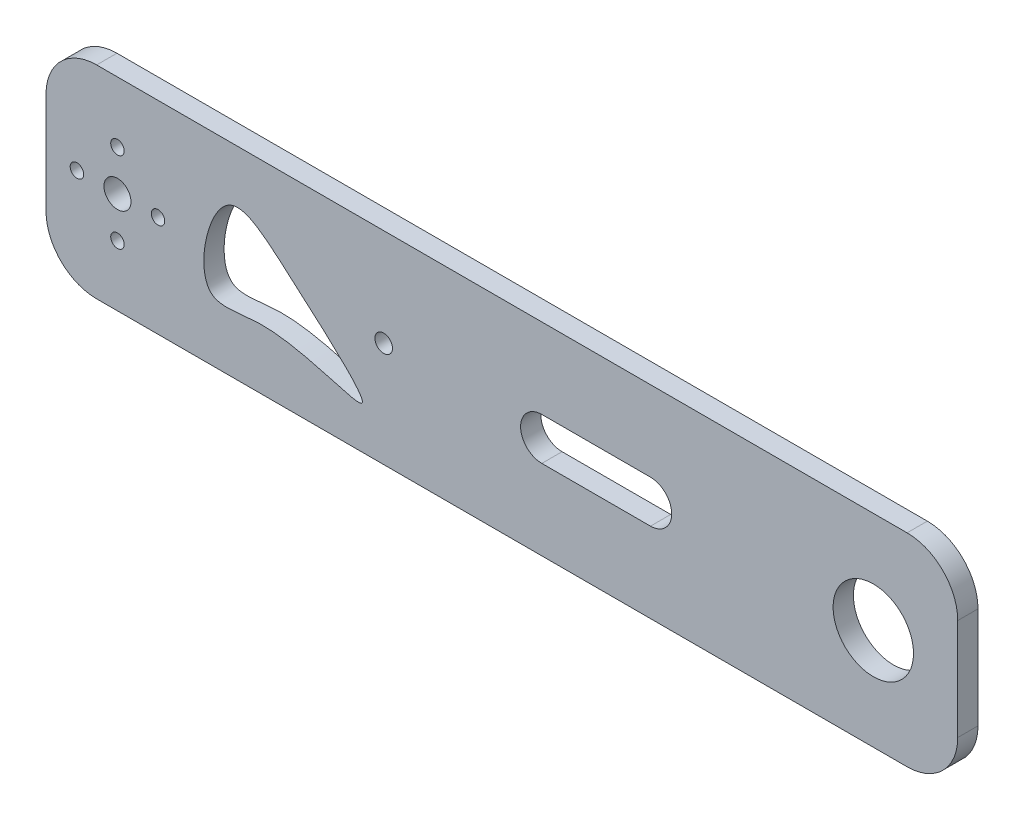
SolidWorks part; units mm, degrees
ref_plane "Front Plane" through (0, 0, 0) normal (0, 0, 1) x (1, 0, 0)
ref_plane "Top Plane" through (0, 0, 0) normal (0, 1, 0) x (1, 0, 0)
ref_plane "Right Plane" through (0, 0, 0) normal (1, 0, 0) x (0, 0, -1)
sketch "Sketch1" plane through (0, 0, 0) normal (0, 0, 1) x (1, 0, 0)
  line L1 (-135, 30) -> (135, 30)
  line L2 (-135, 30) -> (-135, -30)
  line L3 (-135, -30) -> (135, -30)
  line L4 (135, 30) -> (135, -30)
  line L5 (-135, 30) -> (135, -30) construction
  line L6 (-135, -30) -> (135, 30) construction
  point P0 (0, 0)
  dimension "D1" = 270
  dimension "D2" = 60
extrude "Boss-Extrude1" add sketch "Sketch1" along normal mid plane 6
fillet "Fillet1" radius 15 4 edges at (-135, -30, 0) (-135, 30, 0) (135, -30, 0) (135, 30, 0)
sketch "Sketch3" plane through (0, 0, 3) normal (0, 0, 1) x (1, 0, 0)
  line L0 (-133.9593, 0) -> (-95.7585, 0) construction
  line L1 (-113.8353, -15.4334) -> (-113.8353, 22.0078) construction
  circle A0 centre (-113.8353, 0) radius 4
  circle A1 centre (-113.8353, 12) radius 2
  circle A2 centre (-113.8353, -12) radius 2
  circle A3 centre (-101.8353, 0) radius 2
  circle A4 centre (-125.8353, 0) radius 2
  dimension "D1" = 8
  dimension "D2" = 4
  dimension "D4" = 4
  dimension "D3" = 12
  dimension "D5" = 12
extrude "Cut-Extrude1" cut sketch "Sketch3" against normal blind 8
sketch "Sketch4" plane through (0, 0, 3) normal (0, 0, 1) x (1, 0, 0)
  line L0 (-60.7147, 26.838) -> (-9.2853, -24.5914) construction
  line L1 (120, 30) -> (-120, 30) construction
  line L2 (-135, 15) -> (-135, -15) construction
  circle A2 centre (-35, 1.1233) radius 2.6
  circle A3 centre (110, 0) radius 11.9
  dimension "D5" = 5.2
  dimension "D8" = 23.8
  dimension "D4" = 45
  dimension "D7" = 100
  dimension "D9" = 145
extrude "Cut-Extrude2" cut sketch "Sketch4" against normal blind 10
sketch "Sketch5" plane through (0, 0, 3) normal (0, 0, 1) x (1, 0, 0)
  line L0 (11.8296, 0) -> (44.01, 0) construction
  line L1 (11.8296, 6.2805) -> (44.01, 6.2805)
  line L2 (11.8296, -6.2805) -> (44.01, -6.2805)
  arc A0 (11.8296, 6.2805) -> (11.8296, -6.2805) centre (11.8296, 0) ccw
  arc A1 (44.01, -6.2805) -> (44.01, 6.2805) centre (44.01, 0) ccw
  spline S0 degree 3 poles (-65.9298, -8.6177) (-93.1438, -17.1524) (-84.2294, 23.0927) (-60.5625, 2.3907) (-27.0991, -26.623) (-65.9298, -8.6177) (-93.1438, -17.1524) (-84.2294, 23.0927) knots -0.632864 -0.370043 -0.119399 0 0.211869 0.367136 0.629957 0.880601 1 1.211869 1.367136 1.629957 only from (-86.0182, -11.6053) to (-86.0182, -11.6053)
  point P3 (27.9198, 0)
extrude "Cut-Extrude3" cut sketch "Sketch5" against normal blind 10
